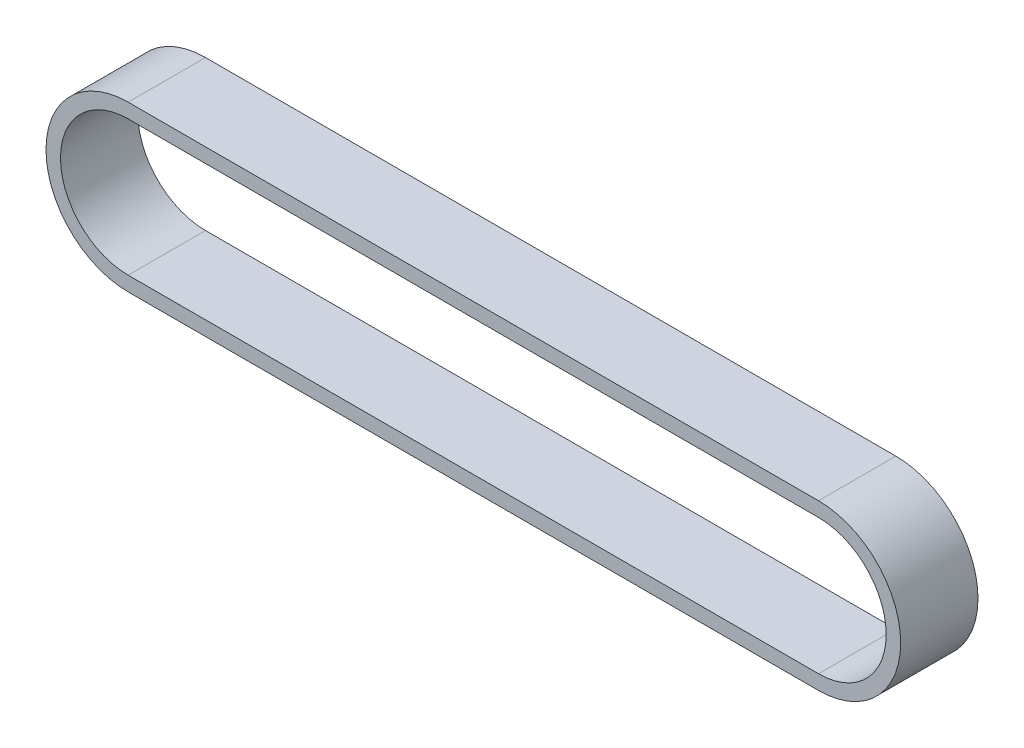
SolidWorks part; units mm, degrees
material "PF"
ref_plane "Piano frontale" through (0, 0, 0) normal (0, 0, 1) x (1, 0, 0)
ref_plane "Piano superiore" through (0, 0, 0) normal (0, 1, 0) x (1, 0, 0)
ref_plane "Piano destro" through (0, 0, 0) normal (1, 0, 0) x (0, 0, -1)
sketch "Schizzo1" plane through (0, 0, 0) normal (0, 0, 1) x (1, 0, 0)
  line L0 (0, 0) -> (-57.1402, 0) construction
  line L1 (0, -5.6) -> (-57.1402, -5.6)
  line L2 (0, 5.6) -> (-57.1402, 5.6)
  line L3 (0, 0) -> (-57.1402, 0) construction
  line L4 (0, -6.8) -> (-57.1402, -6.8)
  line L5 (0, 6.8) -> (-57.1402, 6.8)
  arc A0 (0, -5.6) -> (0, 5.6) centre (0, 0) ccw
  arc A1 (-57.1402, 5.6) -> (-57.1402, -5.6) centre (-57.1402, 0) ccw
  arc A2 (0, -6.8) -> (0, 6.8) centre (0, 0) ccw
  arc A3 (-57.1402, 6.8) -> (-57.1402, -6.8) centre (-57.1402, 0) ccw
  point P3 (-28.5701, 0)
  point P8 (-28.5701, 0)
  line B0 (-57.1402, 0) -> (0, 0) construction
  dimension "D2" = 5.6
  dimension "D1" = 1.2
sketch_block_instance "puleggia piccola_2-1"
sketch_block "puleggia piccola_2"
extrude "Estrusione-Estrusione1" add sketch "Schizzo1" along normal blind 6.4 contours L5 A3 L4 A2 | L2 A1 L1 A0
